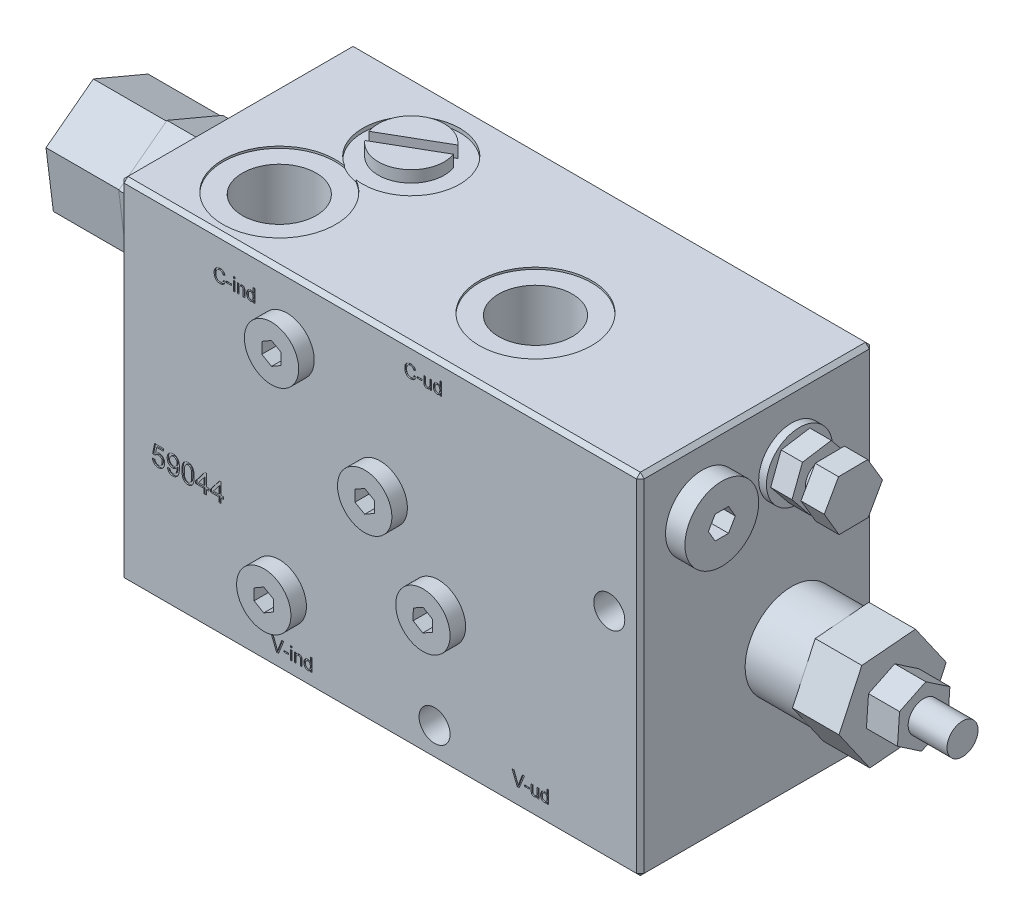
SolidWorks part; units mm, degrees
ref_plane "Plane1" through (0, 0, 0) normal (0, 0, 1) x (1, 0, 0)
ref_plane "Plane2" through (0, 0, 0) normal (0, 1, 0) x (1, 0, 0)
ref_plane "Plane3" through (0, 0, 0) normal (1, 0, 0) x (0, 0, -1)
sketch "Sketch1" plane through (0, 0, 0) normal (0, 0, 1) x (1, 0, 0)
  line L1 (0, 0) -> (134, 0)
  line L2 (0, 0) -> (0, 90)
  line L3 (0, 90) -> (134, 90)
  line L4 (134, 0) -> (134, 90)
  dimension "D1" = 134
  dimension "D2" = 90
extrude "Base-Extrude" add sketch "Sketch1" along normal blind 60
chamfer "Chamfer1" distance 1 angle 45 12 edges at (134, 45, 60) (67, 90, 60) (0, 45, 60) (67, 90, 0) (134, 45, 0) (67, 0, 0) (0, 45, 0) (67, 0, 60) (0, 90, 30) (134, 90, 30) (134, 0, 30) (0, 0, 30)
sketch "Sketch2" plane through (0, 0, 60) normal (0, 0, 1) x (1, 0, 0)
  line L1 (134, 89) -> (134, 1) construction
  line L2 (67, 50.1132) -> (69.5, 51.5566)
  line L3 (69.5, 51.5566) -> (69.5, 54.4434)
  line L4 (69.5, 54.4434) -> (67, 55.8868)
  line L5 (67, 55.8868) -> (64.5, 54.4434)
  line L6 (64.5, 54.4434) -> (64.5, 51.5566)
  line L7 (1, 90) -> (133, 90) construction
  line L8 (64.5, 51.5566) -> (67, 50.1132)
  line L9 (84.4754, 32.5148) -> (84.5239, 35.4011)
  line L10 (84.5239, 35.4011) -> (82.0486, 36.8863)
  line L11 (82.0486, 36.8863) -> (79.5246, 35.4852)
  line L12 (41, 15.1132) -> (43.5, 16.5566)
  line L13 (43.5, 16.5566) -> (43.5, 19.4434)
  line L14 (43.5, 19.4434) -> (41, 20.8868)
  line L15 (41, 20.8868) -> (38.5, 19.4434)
  line L16 (38.5, 19.4434) -> (38.5, 16.5566)
  line L17 (38.5, 16.5566) -> (41, 15.1132)
  line L19 (133, 0) -> (1, 0) construction
  line L20 (43, 76.8868) -> (40.5, 75.4434)
  line L21 (79.5246, 35.4852) -> (79.4761, 32.5989)
  line L22 (79.4761, 32.5989) -> (81.9514, 31.1137)
  line L23 (40.5, 75.4434) -> (40.5, 72.5566)
  line L24 (40.5, 72.5566) -> (43, 71.1132)
  line L25 (43, 71.1132) -> (45.5, 72.5566)
  line L26 (45.5, 72.5566) -> (45.5, 75.4434)
  line L27 (45.5, 75.4434) -> (43, 76.8868)
  line L28 (0, 1) -> (0, 89) construction
  line L33 (81.9514, 31.1137) -> (84.4754, 32.5148)
  circle A0 centre (67, 53) radius 2.5 construction
  circle A1 centre (41, 18) radius 2.5 construction
  circle A2 centre (82, 34) radius 2.5 construction
  circle A3 centre (67, 53) radius 7
  circle A4 centre (82, 34) radius 7
  circle A5 centre (41, 18) radius 7
  circle A6 centre (43, 74) radius 2.5 construction
  circle A7 centre (43, 74) radius 7
  dimension "D7" = 67
  dimension "D9" = 52
  dimension "D10" = 34
  dimension "D6" = 14
  dimension "D12" = 41
  dimension "D13" = 16
  dimension "D14" = 43
  dimension "D3" = 5
  dimension "D8" = 37
  dimension "D11" = 18
extrude "Boss-Extrude1" add sketch "Sketch2" along normal blind 4
sketch "Sketch3" plane through (0, 90, 0) normal (0, 1, 0) x (-1, 0, 0)
  line L0 (-133, 60) -> (-1, 60) construction
  line L3 (0, 59) -> (0, 1) construction
  circle A0 centre (-84, 37) radius 9.5
  circle A1 centre (-24, 43) radius 9.5
  dimension "D2" = 24
  dimension "D5" = 19
  dimension "D3" = 17
  dimension "D1" = 60
  dimension "D4" = 23
extrude "Cut-Extrude1" cut sketch "Sketch3" against normal blind 42
sketch "Sketch4" plane through (0, 48, 0) normal (0, 1, 0) x (-1, 0, 0)
  circle A0 centre (-24, 43) radius 9.5 construction
  circle A1 centre (-84, 37) radius 9.5 construction
  circle A2 centre (-24, 43) radius 9.5
  circle A3 centre (-84, 37) radius 9.5
extrude "Cut-Extrude2" cut sketch "Sketch4" against normal through all draft 60
sketch "Sketch5" plane through (0, 0, 0) normal (0, -1, 0) x (1, 0, 0)
  line L0 (77.25, -12) -> (77.25, 5) construction
  line L3 (0, 1) -> (0, 59) construction
  line L5 (133, 0) -> (1, 0) construction
  circle A0 centre (113.5, 21) radius 9.5
  circle A1 centre (41, 21) radius 9.5
  circle A2 centre (24, 43) radius 9.5 construction
  dimension "D2" = 41
  dimension "D3" = 113.5
  dimension "D1" = 21
extrude "Cut-Extrude3" cut sketch "Sketch5" against normal blind 42
sketch "Sketch6" plane through (0, 42, 0) normal (0, -1, 0) x (1, 0, 0)
  circle A0 centre (41, 21) radius 9.5 construction
  circle A1 centre (113.5, 21) radius 9.5 construction
  circle A2 centre (41, 21) radius 9.5
  circle A3 centre (113.5, 21) radius 9.5
extrude "Cut-Extrude4" cut sketch "Sketch6" against normal through all draft 60
sketch "Sketch7" plane through (0, 0, 0) normal (-1, 0, 0) x (0, 0, 1)
  circle A1 centre (16, 51) radius 13.5
  dimension "D1" = 51
  dimension "D4" = 27
  dimension "D2" = 16
extrude "Boss-Extrude2" add sketch "Sketch7" along normal blind 8
sketch "Sketch8" plane through (-8, 0, 0) normal (-1, 0, 0) x (0, 0, 1)
  line L1 (14.0665, 35.5319) -> (28.429, 41.5915)
  line L2 (28.429, 41.5915) -> (30.3625, 57.0596)
  line L3 (30.3625, 57.0596) -> (17.9335, 66.4681)
  line L4 (17.9335, 66.4681) -> (3.571, 60.4085)
  line L5 (3.571, 60.4085) -> (1.6375, 44.9404)
  line L6 (1.6375, 44.9404) -> (14.0665, 35.5319)
  circle A0 centre (16, 51) radius 13.5 construction
  dimension "D1" = 27
extrude "Boss-Extrude3" add sketch "Sketch8" along normal blind 22
sketch "Sketch9" plane through (134, 0, 0) normal (1, 0, 0) x (0, 0, -1)
  line L0 (-21, 42) -> (-21, 0) construction
  line L1 (-1, 0) -> (-59, 0) construction
  circle A0 centre (-21, 34) radius 12
  dimension "D2" = 24
  dimension "D1" = 34
extrude "Boss-Extrude4" add sketch "Sketch9" along normal blind 14
sketch "Sketch10" plane through (148, 0, 0) normal (1, 0, 0) x (0, 0, -1)
  line L1 (-26.8718, 21.4492) -> (-13.0666, 22.6395)
  line L2 (-13.0666, 22.6395) -> (-7.1948, 35.1903)
  line L3 (-7.1948, 35.1903) -> (-15.1282, 46.5508)
  line L4 (-15.1282, 46.5508) -> (-28.9334, 45.3605)
  line L5 (-28.9334, 45.3605) -> (-34.8052, 32.8097)
  line L6 (-34.8052, 32.8097) -> (-26.8718, 21.4492)
  circle A0 centre (-21, 34) radius 12 construction
  circle A1 centre (-21, 34) radius 12 construction
  dimension "D1" = 24
extrude "Boss-Extrude5" add sketch "Sketch10" along normal blind 12
sketch "Sketch11" plane through (160, 0, 0) normal (1, 0, 0) x (0, 0, -1)
  line L1 (-21.5358, 26.5136) -> (-14.7845, 29.7928)
  line L2 (-14.7845, 29.7928) -> (-14.2487, 37.2792)
  line L3 (-14.2487, 37.2792) -> (-20.4642, 41.4864)
  line L4 (-20.4642, 41.4864) -> (-27.2155, 38.2072)
  line L5 (-27.2155, 38.2072) -> (-27.7513, 30.7208)
  line L6 (-27.7513, 30.7208) -> (-21.5358, 26.5136)
  circle A0 centre (-21, 34) radius 6.5 construction
  circle A1 centre (-21, 34) radius 12 construction
  dimension "D1" = 13
extrude "Boss-Extrude6" add sketch "Sketch11" along normal blind 8
hole_wizard "Hole1" positions "Sketch21" profile "Sketch20" hole size "M6" standard "ISO" end condition through all
sketch "Sketch21" plane through (0, 0, 60) normal (0, 0, 1) x (1, 0, 0)
  line L0 (133, 0) -> (1, 0) construction
  line L1 (134, 89) -> (134, 1) construction
  point P0 (81, 8)
  dimension "D1" = 8
  dimension "D2" = 53
sketch "Sketch20" plane through (81, 8, 60) normal (1, 0, 0) x (0, -1, 0)
  line L0 (0, 0) -> (0, 60)
  line L1 (0, 60) -> (4, 60)
  line L2 (4, 60) -> (4, 0)
  line L5 (4, 0) -> (0, 0)
  line L11 (0, -6.35) -> (0, 107.95) construction
  dimension "Thru Hole Dia." = 8
  dimension "Thru Hole Depth" = 60
hole_wizard "Hole2" positions "Sketch22" profile "Sketch23" hole size "M6" standard "ISO" end condition through all
sketch "Sketch22" plane through (41.551, 37.5449, 60) normal (0, 0, 1) x (1, 0, 0)
  line L2 (92.449, 51.4551) -> (92.449, -36.5449) construction
  circle A1 centre (39.449, -29.5449) radius 4 construction
  point P0 (84.449, 18.4551)
  dimension "D2" = 48
  dimension "D1" = 8
sketch "Sketch23" plane through (126, 56, 60) normal (1, 0, 0) x (0, -1, 0)
  line L0 (0, 0) -> (0, 60)
  line L1 (0, 60) -> (4, 60)
  line L2 (4, 60) -> (4, 0)
  line L5 (4, 0) -> (0, 0)
  line L11 (0, -6.35) -> (0, 107.95) construction
  dimension "Thru Hole Dia." = 8
  dimension "Thru Hole Depth" = 60
sketch "Sketch13" plane through (0, 0, 60) normal (0, 0, 1) x (1, 0, 0)
  text T0 "C-ind" font "Arial" height 3.5
extrude "C-ind" cut sketch "Sketch13" against normal blind 0.3
sketch "Sketch14" plane through (0, 0, 60) normal (0, 0, 1) x (1, 0, 0)
  text T0 "C-ud" font "Arial" height 3.5
extrude "C-ud" cut sketch "Sketch14" against normal blind 0.3
sketch "Sketch15" plane through (0, 0, 60) normal (0, 0, 1) x (1, 0, 0)
  text T0 "V-ind"
extrude "V-ind" cut sketch "Sketch15" against normal blind 0.3
sketch "Sketch16" plane through (0, 0, 60) normal (0, 0, 1) x (1, 0, 0)
  text T0 "V-ud"
extrude "V-ud" cut sketch "Sketch16" against normal blind 0.3
sketch "Sketch24" plane through (0, 0, 60) normal (0, 0, 1) x (1, 0, 0)
  text T0 "59044" font "Arial" height in points 20
extrude "59044" cut sketch "Sketch24" against normal blind 0.3
sketch "Sketch25" plane through (0, 90, 0) normal (0, 1, 0) x (-1, 0, 0)
  line L0 (-1, 0) -> (-133, 0) construction
  line L1 (0, 59) -> (0, 1) construction
  line L2 (-25.0043, 20.8843) -> (-39.4957, 12.5177)
  line L3 (-26.5043, 23.4823) -> (-40.9957, 15.1157)
  arc A0 (-39.4957, 12.5177) -> (-25.0043, 20.8843) centre (-33, 18) ccw
  arc A1 (-26.5043, 23.4823) -> (-40.9957, 15.1157) centre (-33, 18) ccw
  dimension "D1" = 17
  dimension "D2" = 18
  dimension "D3" = 33
  dimension "D4" = 3
  dimension "D5" = 30
extrude "Boss-Extrude7" add sketch "Sketch25" along normal blind 3
sketch "Sketch26" plane through (0, 0, 0) normal (-1, 0, 0) x (0, 0, 1)
  line L0 (60, 89) -> (60, 1) construction
  line L1 (49.0412, 50.9588) -> (49.7884, 53.7471)
  line L2 (49.7884, 53.7471) -> (47.7471, 55.7884)
  line L3 (47.7471, 55.7884) -> (44.9588, 55.0412)
  line L4 (44.9588, 55.0412) -> (44.2116, 52.2529)
  line L5 (44.2116, 52.2529) -> (46.2529, 50.2116)
  line L6 (46.2529, 50.2116) -> (49.0412, 50.9588)
  line L7 (1, 90) -> (59, 90) construction
  circle A0 centre (47, 53) radius 2.5 construction
  circle A1 centre (47, 53) radius 7
  dimension "D1" = 14
  dimension "D3" = 13
  dimension "D4" = 37
  dimension "D2" = 5
extrude "Boss-Extrude8" add sketch "Sketch26" along normal blind 3
sketch "Sketch27" plane through (0, 0, 0) normal (-1, 0, 0) x (0, 0, 1)
  line L0 (60, 89) -> (60, 1) construction
  line L1 (59, 0) -> (1, 0) construction
  circle A0 centre (45, 18) radius 12.3
  dimension "D1" = 24.6
  dimension "D2" = 15
  dimension "D3" = 18
extrude "Cut-Extrude10" cut sketch "Sketch27" against normal blind 9
sketch "Sketch28" plane through (9, 0, 0) normal (-1, 0, 0) x (0, 0, 1)
  line L0 (45, 8) -> (45, 29) construction
  line L1 (46.5, 26.3666) -> (46.5, 9.6334)
  line L2 (43.5, 26.3666) -> (43.5, 9.6334)
  arc A0 (43.5, 26.3666) -> (43.5, 9.6334) centre (45, 18) ccw
  circle A2 centre (45, 18) radius 12.3 construction
  arc A3 (46.5, 9.6334) -> (46.5, 26.3666) centre (45, 18) ccw
  dimension "D1" = 17
  dimension "D2" = 3
extrude "Boss-Extrude9" add sketch "Sketch28" along normal blind 5
sketch "Sketch29" plane through (-30, 0, 0) normal (-1, 0, 0) x (0, 0, 1)
  line L0 (17.9335, 66.4681) -> (3.571, 60.4085) construction
  line L1 (14.1023, 35.8184) -> (28.1988, 41.7657)
  line L2 (28.1988, 41.7657) -> (30.0965, 56.9474)
  line L3 (30.0965, 56.9474) -> (17.8977, 66.1816)
  line L4 (17.8977, 66.1816) -> (3.8012, 60.2343)
  line L5 (3.8012, 60.2343) -> (1.9035, 45.0526)
  line L6 (1.9035, 45.0526) -> (14.1023, 35.8184)
  circle A0 centre (16, 51) radius 13.25 construction
  dimension "D1" = 26.5
extrude "Boss-Extrude10" add sketch "Sketch29" along normal blind 19
sketch "Sketch31" plane through (134, 0, 0) normal (1, 0, 0) x (0, 0, -1)
  line L0 (-59, 90) -> (-1, 90) construction
  line L1 (-60, 1) -> (-60, 89) construction
  line L3 (-40.5359, 74) -> (-42.2679, 77)
  line L4 (-42.2679, 77) -> (-45.7321, 77)
  line L5 (-45.7321, 77) -> (-47.4641, 74)
  line L6 (-47.4641, 74) -> (-45.7321, 71)
  line L7 (-45.7321, 71) -> (-42.2679, 71)
  line L8 (-42.2679, 71) -> (-40.5359, 74)
  circle A0 centre (-44, 74) radius 9.5
  circle A1 centre (-44, 74) radius 3 construction
  dimension "D1" = 19
  dimension "D2" = 16
  dimension "D3" = 16
  dimension "D4" = 6
extrude "Boss-Extrude11" add sketch "Sketch31" along normal blind 5
sketch "Sketch33" plane through (134, 0, 0) normal (1, 0, 0) x (0, 0, -1)
  line L0 (0, 89) -> (0, 1) construction
  line L1 (-59, 90) -> (-1, 90) construction
  circle A0 centre (-21, 74) radius 8.5
  dimension "D1" = 17
  dimension "D2" = 21
  dimension "D3" = 16
extrude "Boss-Extrude12" add sketch "Sketch33" along normal blind 2
sketch "Sketch34" plane through (136, 0, 0) normal (1, 0, 0) x (0, 0, -1)
  line L0 (-21, 42) -> (-21, 0) construction
  line L1 (-16.2791, 68.1651) -> (-13.5863, 75.1709)
  line L2 (-13.5863, 75.1709) -> (-18.3072, 81.0059)
  line L3 (-18.3072, 81.0059) -> (-25.7209, 79.8349)
  line L4 (-25.7209, 79.8349) -> (-28.4137, 72.8291)
  line L5 (-28.4137, 72.8291) -> (-23.6928, 66.9941)
  line L6 (-23.6928, 66.9941) -> (-16.2791, 68.1651)
  circle A0 centre (-21, 74) radius 6.5 construction
  circle A1 centre (-21, 74) radius 8.5 construction
  dimension "D1" = 13
extrude "Boss-Extrude13" add sketch "Sketch34" along normal blind 5.5
sketch "Sketch36" plane through (141.5, 0, 0) normal (1, 0, 0) x (0, 0, -1)
  line L0 (-21, 42) -> (-21, 0) construction
  circle A0 centre (-21, 74) radius 4
  circle A1 centre (-21, 74) radius 8.5 construction
  dimension "D1" = 8
extrude "Boss-Extrude14" add sketch "Sketch36" along normal blind 8.5
sketch "Sketch37" plane through (168, 0, 0) normal (1, 0, 0) x (0, 0, -1)
  line L0 (-64, 34) -> (-60, 34) construction
  circle A0 centre (-21, 34) radius 4
  circle A1 centre (-21, 34) radius 12 construction
  dimension "D1" = 8
extrude "Boss-Extrude15" add sketch "Sketch37" along normal blind 10
sketch "Sketch41" plane through (150, 0, 0) normal (1, 0, 0) x (0, 0, -1)
  line L0 (-64, 74) -> (-60, 74) construction
  line L1 (-17.2836, 67.5426) -> (-13.6041, 74.0844)
  line L2 (-13.6041, 74.0844) -> (-17.4297, 80.5418)
  line L3 (-17.4297, 80.5418) -> (-24.9348, 80.4574)
  line L4 (-24.9348, 80.4574) -> (-28.6143, 73.9156)
  line L5 (-28.6143, 73.9156) -> (-24.7887, 67.4582)
  line L6 (-24.7887, 67.4582) -> (-17.2836, 67.5426)
  circle A0 centre (-21.1092, 74) radius 6.5 construction
  dimension "D1" = 13
extrude "Boss-Extrude19" add sketch "Sketch41" against normal blind 6
sketch "Sketch42" plane through (0, 90, 0) normal (0, 1, 0) x (-1, 0, 0)
  circle A0 centre (-33, 18) radius 12.5
  arc A1 (-26.5043, 23.4823) -> (-40.9957, 15.1157) centre (-33, 18) ccw construction
  dimension "D1" = 25
extrude "Cut-Extrude11" cut sketch "Sketch42" against normal blind 1
sketch "Sketch43" plane through (0, 90, 0) normal (0, 1, 0) x (-1, 0, 0)
  circle A0 centre (-24, 43) radius 14.5
  circle A1 centre (-24, 43) radius 9.5 construction
  circle A2 centre (-84, 37) radius 14.5
  circle A3 centre (-84, 37) radius 9.5 construction
  dimension "D1" = 29
extrude "Cut-Extrude12" cut sketch "Sketch43" against normal blind 0.5
